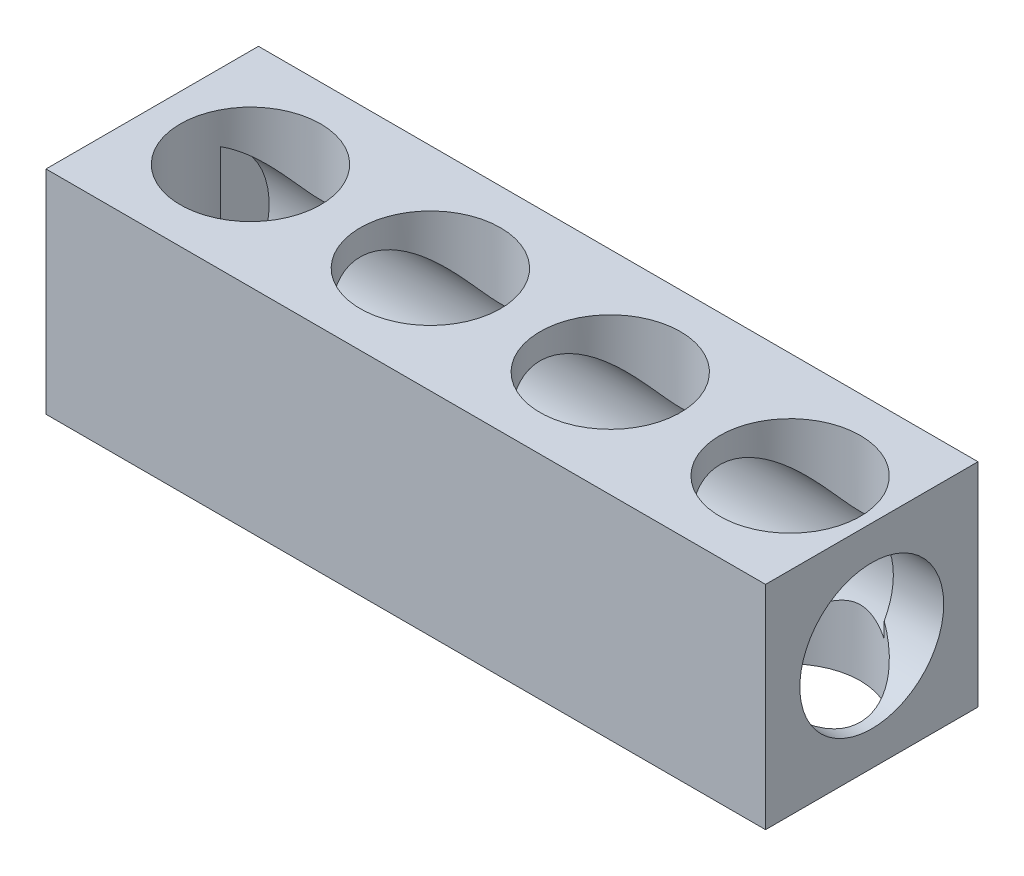
SolidWorks part; units mm, degrees
ref_plane "Front Plane" through (0, 0, 0) normal (0, 0, 1) x (1, 0, 0)
ref_plane "Top Plane" through (0, 0, 0) normal (0, 1, 0) x (1, 0, 0)
ref_plane "Right Plane" through (0, 0, 0) normal (1, 0, 0) x (0, 0, -1)
sketch "Sketch1" plane through (0, 0, 0) normal (1, 0, 0) x (0, 0, -1)
  line L1 (-7.5, -7.5) -> (7.5, -7.5)
  line L2 (-7.5, -7.5) -> (-7.5, 7.5)
  line L3 (-7.5, 7.5) -> (7.5, 7.5)
  line L4 (7.5, -7.5) -> (7.5, 7.5)
  line L5 (-7.5, -7.5) -> (7.5, 7.5) construction
  line L6 (-7.5, 7.5) -> (7.5, -7.5) construction
  point P0 (0, 0)
  dimension "D1" = 15
  dimension "D2" = 15
extrude "Boss-Extrude1" add sketch "Sketch1" against normal blind 50.8
ref_plane "Plane1" through (-48.26, 0, 0) normal (-1, 0, 0) x (0, 0, 1)
sketch "Sketch3" plane through (-48.26, 0, 0) normal (-1, 0, 0) x (0, 0, 1)
  circle A0 centre (0, 0) radius 5.715
  dimension "D1" = 11.43
extrude "Cut-Extrude1" cut sketch "Sketch3" against normal blind 44.704
sketch "Sketch4" plane through (0, 0, 0) normal (1, 0, 0) x (0, 0, -1)
  circle A0 centre (0, 0) radius 5.08
  dimension "D1" = 10.16
sketch "Sketch5" plane through (0, -7.5, 0) normal (0, -1, 0) x (-1, 0, 0)
  circle A0 centre (43.8634, 0) radius 4.953
  dimension "D1" = 9.906
extrude "Cut-Extrude3" cut sketch "Sketch5" against normal through all
pattern_linear "LPattern1" count 4 spacing 12.7 along (1, 0, 0) of "Cut-Extrude3"
extrude "Cut-Extrude5" cut sketch "Sketch4" against normal blind 6.096
